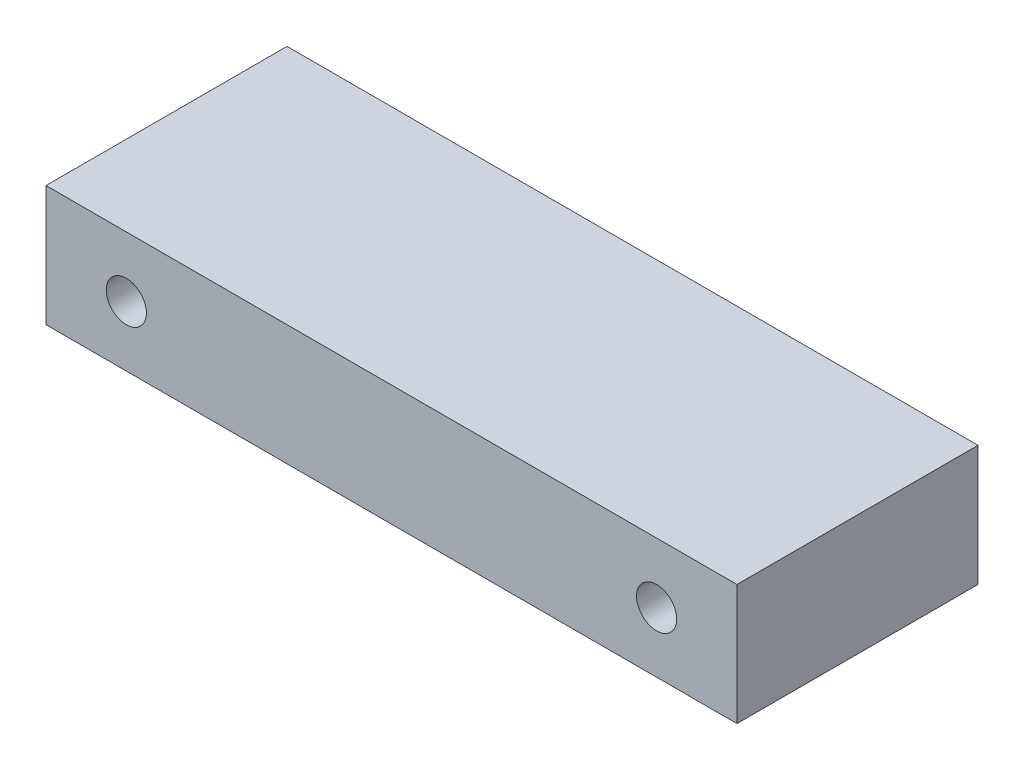
SolidWorks part; units mm, degrees
ref_plane "Front Plane" through (0, 0, 0) normal (0, 0, 1) x (1, 0, 0)
ref_plane "Top Plane" through (0, 0, 0) normal (0, 1, 0) x (1, 0, 0)
ref_plane "Right Plane" through (0, 0, 0) normal (1, 0, 0) x (0, 0, -1)
ref_plane "Plane4"
sketch "Sketch1" plane through (0, 0, 0) normal (0, 0, 1) x (1, 0, 0)
  line L0 (109.22, 19.05) -> (0, 19.05)
  line L1 (0, 19.05) -> (0, 0)
  line L2 (0, 0) -> (109.22, 0)
  line L3 (109.22, 0) -> (109.22, 19.05)
  circle A0 centre (12.7, 9.525) radius 3.175
  circle A1 centre (96.52, 9.525) radius 3.175
  dimension "D2" = 6.35
  dimension "D3" = 6.35
  dimension "D1" = 19.05
  dimension "D4" = 83.82
  dimension "D5" = 109.22
extrude "Extrusion1" add sketch "Sketch1" along normal blind 38.1 contours L2 L3 L0 L1 A1 A0
